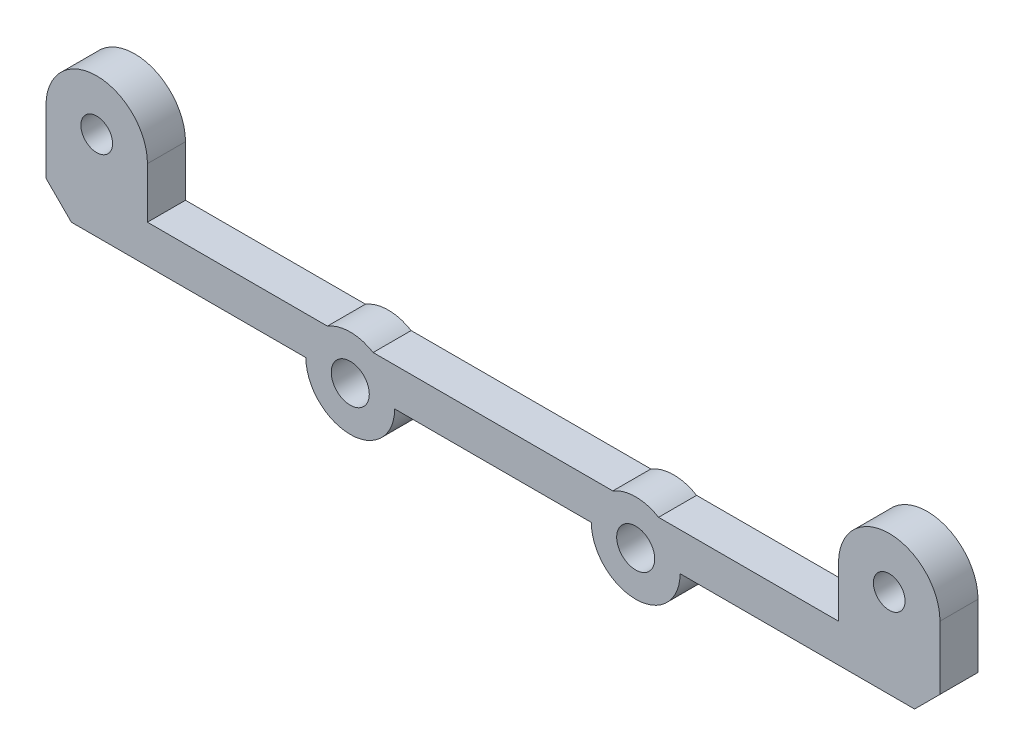
SolidWorks part; units mm, degrees
ref_plane "前视基准面" through (0, 0, 0) normal (0, 0, 1) x (1, 0, 0)
ref_plane "上视基准面" through (0, 0, 0) normal (0, 1, 0) x (1, 0, 0)
ref_plane "右视基准面" through (0, 0, 0) normal (1, 0, 0) x (0, 0, -1)
sketch "草图1" plane through (0, 0, 0) normal (0, 0, 1) x (1, 0, 0)
  line L0 (3.5, 0) -> (19.01, 0)
  line L1 (26.01, 0) -> (44.505, 0)
  line L2 (24.3128, 3) -> (38.505, 3)
  line L3 (1.8028, 3) -> (20.7072, 3)
  line L4 (-15.995, 7) -> (-15.995, 3)
  line L5 (-15.995, 3) -> (-1.8028, 3)
  line L6 (38.505, 3) -> (38.505, 7)
  line L8 (-23.995, 7) -> (-23.995, 2)
  line L9 (-21.995, 0) -> (-3.5, 0)
  line L10 (46.505, 2) -> (46.505, 7)
  line L11 (-23.995, 2) -> (-21.995, 0)
  line L12 (46.505, 2) -> (44.505, 0)
  circle A0 centre (22.51, 0) radius 1.5
  circle A1 centre (0, 0) radius 1.5
  circle A2 centre (-19.995, 7) radius 1.25
  circle A3 centre (42.505, 7) radius 1.25
  arc A4 (-15.995, 7) -> (-23.995, 7) centre (-19.995, 7) ccw
  arc A5 (46.505, 7) -> (38.505, 7) centre (42.505, 7) ccw
  arc A6 (-3.5, 0) -> (3.5, 0) centre (0, 0) ccw
  arc A7 (19.01, 0) -> (26.01, 0) centre (22.51, 0) ccw
  arc A8 (24.3128, 3) -> (20.7072, 3) centre (22.51, 0) ccw
  arc A9 (1.8028, 3) -> (-1.8028, 3) centre (0, 0) ccw
extrude "凸台-拉伸2" add sketch "草图1" along normal blind 3
